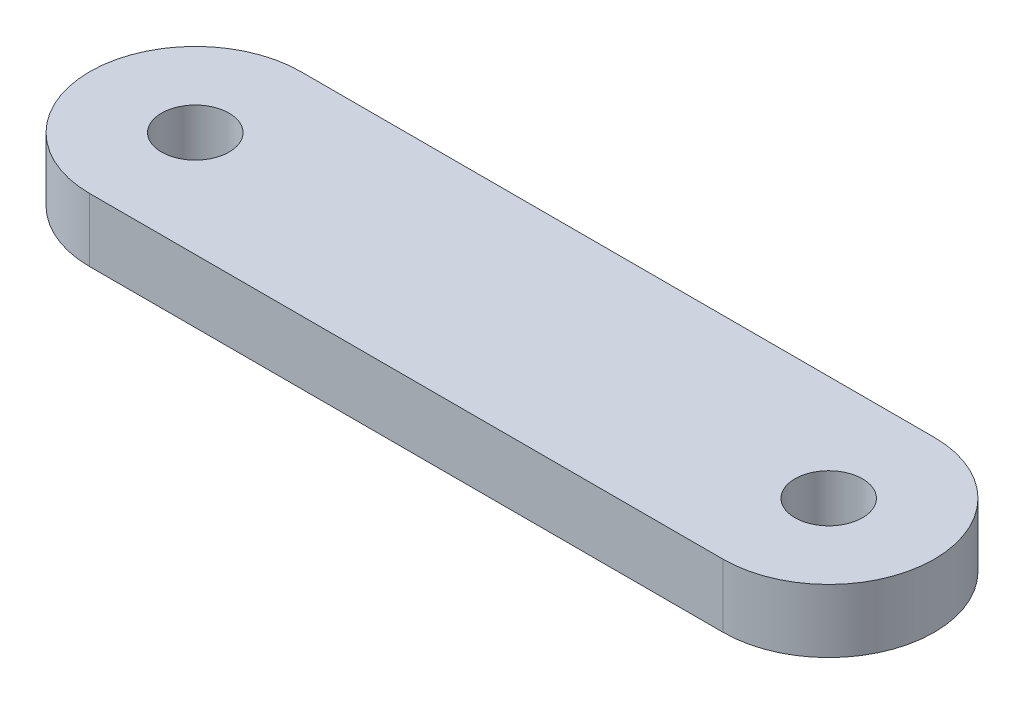
SolidWorks part; units mm, degrees
material "Thornel Mat VMA"
ref_plane "前视基准面" through (0, 0, 0) normal (0, 0, 1) x (1, 0, 0)
ref_plane "上视基准面" through (0, 0, 0) normal (0, 1, 0) x (1, 0, 0)
ref_plane "右视基准面" through (0, 0, 0) normal (1, 0, 0) x (0, 0, -1)
sketch "草图1" plane through (0, 0, 0) normal (0, 1, 0) x (1, 0, 0)
  line L0 (0, 0) -> (-30, 0) construction
  line L1 (-30, 0) -> (0, 0) construction
  line L2 (-30, 5) -> (0, 5)
  line L3 (-30, -5) -> (0, -5)
  arc A0 (-30, 5) -> (-30, -5) centre (-30, 0) ccw
  arc A1 (0, -5) -> (0, 5) centre (0, 0) ccw
  circle A2 centre (-30, 0) radius 1.6
  circle A3 centre (0, 0) radius 1.6
  point P3 (-15, 0)
  dimension "D2" = 3.2
  dimension "D3" = 3.2
  dimension "D1" = 30
extrude "凸台-拉伸1" add sketch "草图1" along normal blind 3
